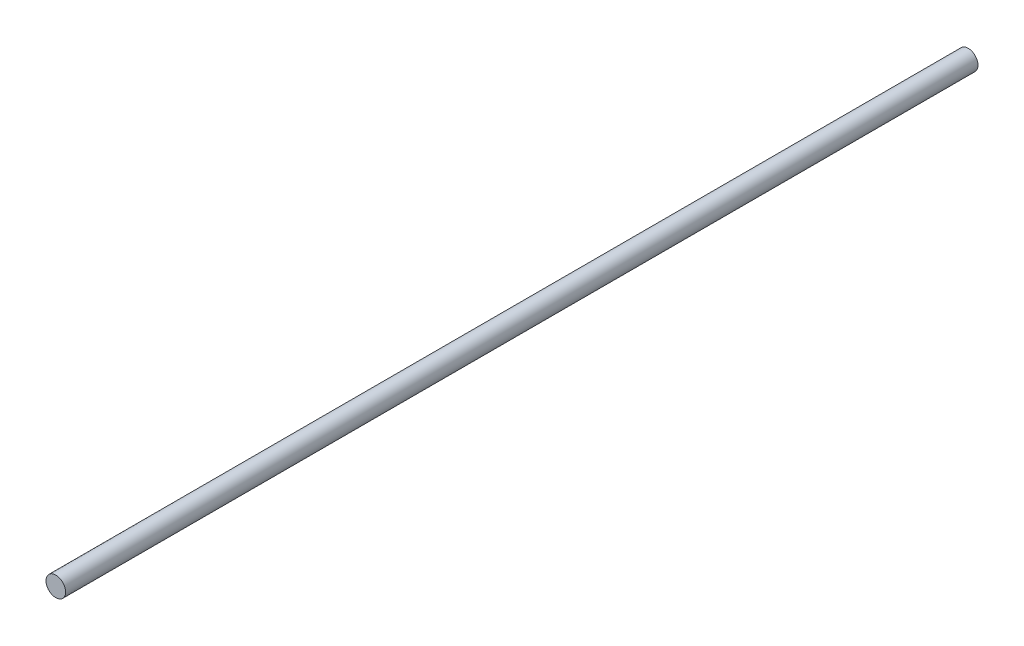
SolidWorks part; units mm, degrees
ref_plane "Front Plane" through (0, 0, 0) normal (0, 0, 1) x (1, 0, 0)
ref_plane "Top Plane" through (0, 0, 0) normal (0, 1, 0) x (1, 0, 0)
ref_plane "Right Plane" through (0, 0, 0) normal (1, 0, 0) x (0, 0, -1)
sketch "Sketch1" plane through (0, 0, 0) normal (0, 0, 1) x (1, 0, 0)
  circle A0 centre (0, 0) radius 4
  dimension "D1" = 8
extrude "Boss-Extrude1" add sketch "Sketch1" along normal blind 372
